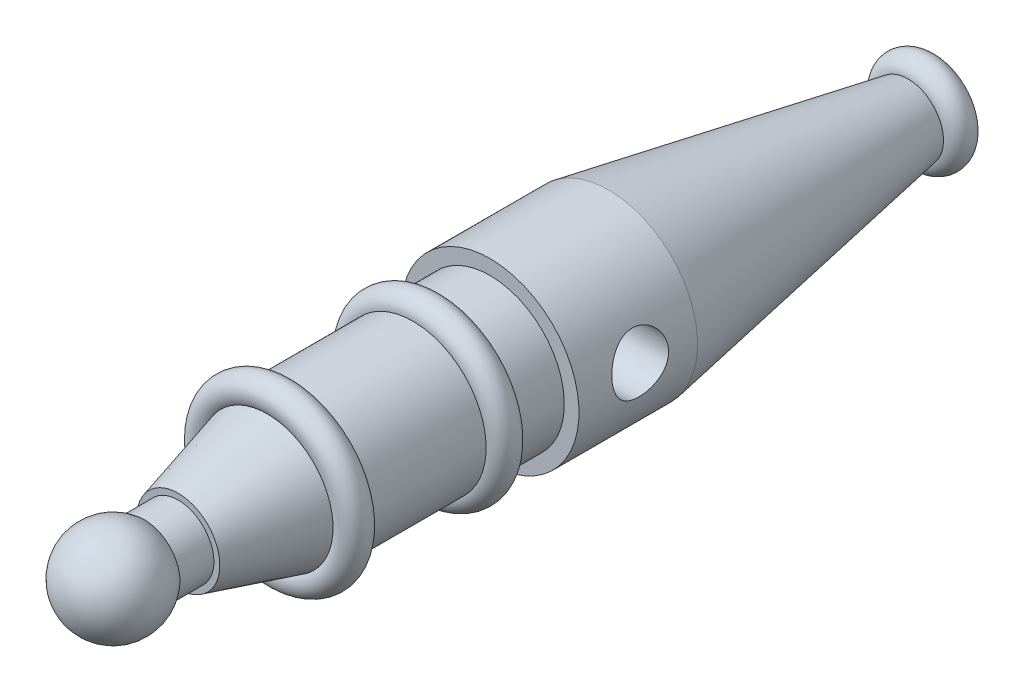
SolidWorks part; units mm, degrees
ref_plane "Front Plane" through (0, 0, 0) normal (0, 0, 1) x (1, 0, 0)
ref_plane "Top Plane" through (0, 0, 0) normal (0, 1, 0) x (1, 0, 0)
ref_plane "Right Plane" through (0, 0, 0) normal (1, 0, 0) x (0, 0, -1)
sketch "Sketch1" plane through (0, 0, 0) normal (1, 0, 0) x (0, 0, -1)
  line L0 (-48.8975, 0) -> (90.1025, 0) construction
  line L1 (-37.8975, 6) -> (-37.8975, 7)
  line L6 (-43.606, 6) -> (-37.8975, 6)
  line L10 (90.1025, 0) -> (-56.8975, 0)
  line L12 (-37.8975, 7) -> (-22.8975, 11.097)
  line L13 (-18.3332, 12.3437) -> (1.6668, 12.3437)
  line L14 (6.6618, 12.5254) -> (14.6618, 12.5254)
  line L15 (14.6618, 12.5254) -> (14.6618, 14.9983)
  line L16 (90.1025, 5.8022) -> (90.1025, 0)
  line L17 (14.6618, 14.9983) -> (34.6618, 14.9983)
  line L18 (34.6618, 14.9983) -> (85.1103, 6)
  line L19 (-48.8975, 0) -> (-56.8975, 0) construction
  arc A1 (-22.8975, 11.097) -> (-18.3332, 12.3437) centre (-20.8283, 12.5) cw
  arc A2 (1.6668, 12.3437) -> (6.6618, 12.5254) centre (4.1619, 12.5) cw
  arc A3 (85.1103, 6) -> (90.1025, 5.8022) centre (87.6025, 5.8022) cw
  arc A4 (-43.606, 6) -> (-56.8975, 0) centre (-48.8975, 0) ccw
  point P4 (-54.4886, 0)
  point P5 (-40.7518, 0)
  point P24 (4.0711, 14.9983)
  point P27 (-60.3223, 7.9322)
  dimension "D4" = 147
  dimension "D6" = 20
  dimension "D7" = 2.5
  dimension "D8" = 25
  dimension "D5" = 14
  dimension "D9" = 4.9983
  dimension "D10" = 15
  dimension "D11" = 8
  dimension "D12" = 20
  dimension "D13" = 6
revolve "Revolve2" add sketch "Sketch1" angle 360 about L10
sketch "Sketch2" plane through (0, 0, -90.1025) normal (0, 0, -1) x (-1, 0, 0)
  circle A0 centre (0, 0) radius 5.8022
extrude "Cut-Extrude1" cut sketch "Sketch2" against normal blind 50
sketch "Sketch3" plane through (0, 0, 0) normal (1, 0, 0) x (0, 0, -1)
  circle A0 centre (25.0834, 1.6789) radius 4.75
  arc A1 (-43.606, 6) -> (-43.606, -6) centre (-48.8975, 0) ccw construction
  dimension "D1" = 9.5
  dimension "D2" = 74
extrude "Cut-Extrude2" cut sketch "Sketch3" against normal through all both and the other way through all
